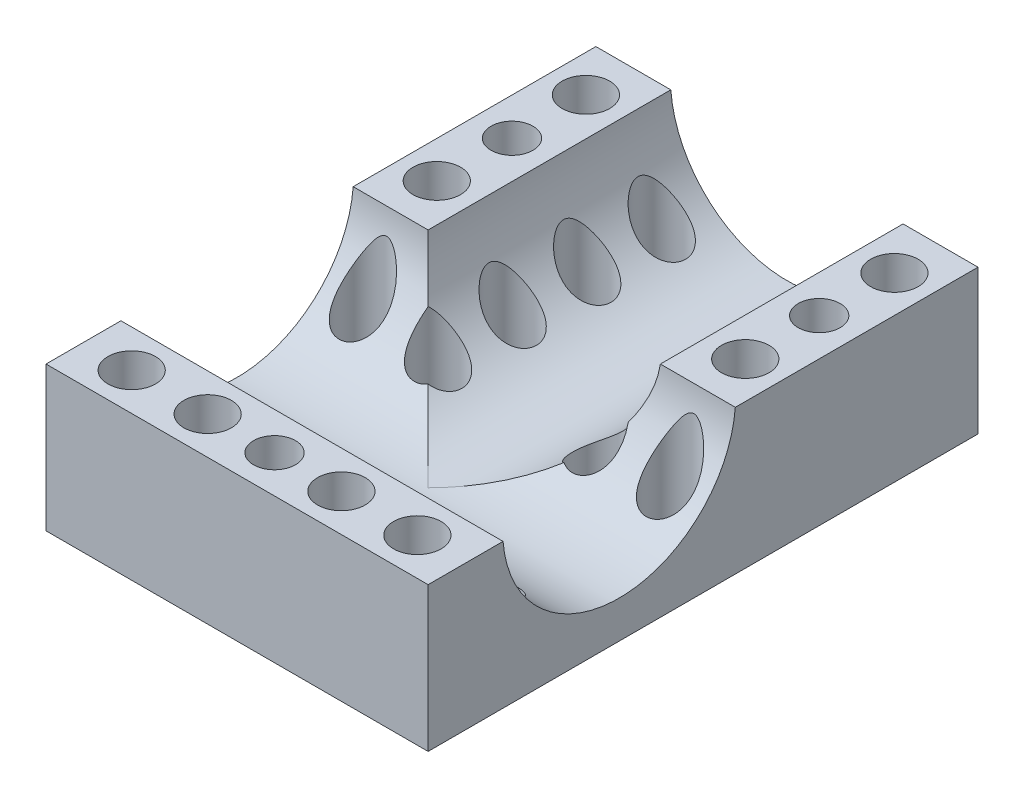
SolidWorks part; units mm, degrees
material "3.1355 (EN-AW 2024)"
ref_plane "Front" through (0, 0, 0) normal (0, 0, 1) x (1, 0, 0)
ref_plane "Top" through (0, 0, 0) normal (0, 1, 0) x (1, 0, 0)
ref_plane "Right" through (0, 0, 0) normal (1, 0, 0) x (0, 0, -1)
sketch "Эскиз1" plane through (0, 0, 0) normal (0, 1, 0) x (1, 0, 0)
  line L0 (0, 0) -> (8, 0)
  line L1 (8, 0) -> (33, 0)
  line L2 (33, 0) -> (41, 0)
  line L3 (0, 0) -> (0, 8)
  line L4 (0, 8) -> (0, 33)
  line L5 (0, 33) -> (0, 41)
  line L6 (0, 41) -> (0, 51)
  line L7 (0, 51) -> (0, 59)
  line L8 (0, 59) -> (41, 59)
  line L9 (41, 59) -> (41, 0)
  dimension "D1" = 8
  dimension "D2" = 25
  dimension "D3" = 8
  dimension "D4" = 8
  dimension "D5" = 25
  dimension "D6" = 8
  dimension "D7" = 10
  dimension "D8" = 8
extrude "Бобышка-Вытянуть1" add sketch "Эскиз1" along normal blind 15.5
sketch "Эскиз4" plane through (0, 0, 0) normal (-1, 0, 0) x (0, 0, 1)
  line L0 (-33, 0) -> (-8, 0) construction
  line L1 (-33, 0) -> (-41, 0) construction
  line L2 (-8, 0) -> (-33, 0) construction
  line L3 (-20.5, 0) -> (-20.5, 16.5) construction
  line L4 (-59, 15.5) -> (0, 15.5) construction
  line L5 (-33, 16.5) -> (-8, 16.5)
  line L6 (-20.5, 16.5) -> (-20.5, 15.5) construction
  arc A0 (-33, 16.5) -> (-8, 16.5) centre (-20.5, 16.5) ccw
  dimension "D1" = 12.5
  dimension "D2" = 1
extrude "Вырез-Вытянуть1" cut sketch "Эскиз4" against normal through all
sketch "Эскиз5" plane through (0, 0, -59) normal (0, 0, -1) x (-1, 0, 0)
  line L0 (-20.5, 16.5) -> (-20.5, 0) construction
  line L2 (0, 0) -> (-41, 0) construction
  line L3 (-33, 16.5) -> (-8, 16.5)
  line L4 (-41, 15.5) -> (0, 15.5) construction
  arc A0 (-33, 16.5) -> (-8, 16.5) centre (-20.5, 16.5) ccw
  dimension "D1" = 12.5
  dimension "D2" = 1
extrude "Вырез-Вытянуть2" cut sketch "Эскиз5" against normal blind 38.5
sketch "Эскиз7" plane through (0, 0, 0) normal (0, -1, 0) x (1, 0, 0)
  line L4 (41, 0) -> (0, 0)
  line L5 (0, 0) -> (0, -59)
  line L6 (0, -59) -> (41, -59)
  line L7 (41, -59) -> (41, 0)
  line L8 (41, 0) -> (0, 0)
  line L9 (0, 0) -> (0, -59)
  line L10 (0, -59) -> (41, -59)
  line L11 (41, -59) -> (41, 0)
  dimension "D1" = 0
ref_plane "Плоскость1" through (0, 4, 0) normal (0, 1, 0) x (1, 0, 0)
sketch "Эскиз6" plane through (0, 4, 0) normal (0, -1, 0) x (1, 0, 0)
  line L0 (20.5, -8.0401) -> (20.5, -32.9599) construction
  line L1 (41, -8.0401) -> (0, -8.0401) construction
  line L2 (0, -32.9599) -> (41, -32.9599) construction
  circle A0 centre (20.5, -20.5) radius 6 construction
  point P11 (20.5, -14.5)
  point P12 (26.5, -20.5)
  point P13 (20.5, -26.5)
  point P14 (14.5, -20.5)
  dimension "D1" = 12
extrude "Бобышка-Вытянуть2" [suppressed] add sketch "Эскиз7" along normal blind 4
sketch "Эскиз14" [suppressed] plane through (0, 2.9, 0) normal (0, 1, 0) x (1, 0, 0)
  circle A0 centre (20.5, 26.5) radius 4
  circle A1 centre (26.5, 20.5) radius 4
  circle A2 centre (20.5, 14.5) radius 4
  circle A3 centre (14.5, 20.5) radius 4
  point P12 (20.5, 20.5)
  dimension "D1" = 8
  dimension "D2" = 4
extrude "Вырез-Вытянуть3" [suppressed] cut sketch "Эскиз14" along normal through all
hole_wizard "Цековка для винта с внутренним шестигранником M44" [suppressed] positions "Эскиз19" profile "Эскиз15" counterbore size "M4" standard "Ansi Metric"
sketch "Эскиз19" [suppressed] plane through (0, 2.9, 0) normal (0, 1, 0) x (1, 0, 0)
  point P0 (14.5, 20.5)
  point P3 (20.5, 26.5)
  point P6 (26.5, 20.5)
  point P9 (20.5, 14.5)
sketch "Эскиз15" plane through (14.5, 2.9, -20.5) normal (1, 0, 0) x (0, 0, 1)
  line L0 (0, 0) -> (0, 6.9)
  line L1 (0, 6.9) -> (2.25, 6.9)
  line L3 (2.25, 6.9) -> (2.25, 4)
  line L4 (2.25, 4) -> (4, 4)
  line L5 (4, 4) -> (4, 0)
  line L7 (4, 0) -> (0, 0)
  line L11 (0, -6.35) -> (0, 107.95) construction
  dimension "Диаметр сквозного отверстия" = 4.5
  dimension "Глубина сквозного отверстия" = 6.9
  dimension "Диаметр цековки" = 8
  dimension "Глубина цековки" = 4
sketch "Эскиз20" plane through (0, 15.5, 0) normal (0, 1, 0) x (1, 0, 0)
  line L1 (4.02, 59) -> (4.02, 32.9599) construction
  line L2 (8.0401, 59) -> (0, 59) construction
  line L3 (0, 32.9599) -> (41, 32.9599) construction
  line L4 (20.5, 59) -> (20.5, 8.0401) construction
  line L5 (32.9599, 59) -> (8.0401, 59) construction
  line L6 (0, 20.5) -> (41, 20.5) construction
  line L7 (0, 32.9599) -> (0, 8.0401) construction
  line L8 (41, 8.0401) -> (41, 32.9599) construction
  line L9 (0, 4.02) -> (41, 4.02) construction
  line L10 (0, 8.0401) -> (0, 0) construction
  line L11 (41, 0) -> (41, 8.0401) construction
  point P17 (4.02, 45.98)
  point P18 (36.98, 45.98)
  point P25 (20.5, 4.02)
  point P26 (-7.3564, 17.7008)
hole_wizard "Отверстие обработанное метчиком M4x0.71" positions "Эскиз22" profile "Эскиз21" tap size "M4x0.7" standard "Ansi Metric" end condition through all
sketch "Эскиз22" plane through (0, 15.5, 0) normal (0, 1, 0) x (1, 0, 0)
  point P0 (4.02, 45.98)
  point P3 (36.98, 45.98)
  point P6 (20.5, 4.02)
sketch "Эскиз21" plane through (4.02, 15.5, -45.98) normal (1, 0, 0) x (0, 0, 1)
  line L0 (0, 0) -> (0, 15.5)
  line L1 (0, 15.5) -> (1.65, 15.5)
  line L2 (1.65, 15.5) -> (1.65, 0)
  line L5 (1.65, 0) -> (0, 0)
  line L11 (0, -6.35) -> (0, 107.95) construction
  dimension "Диаметр проходного сверла" = 3.3
  dimension "Глубина проходного сверла" = 15.5
cosmetic thread "Отверстие резьбы1" parameters "D2"=4
cosmetic thread "Отверстие резьбы2" parameters "D2"=4
cosmetic thread "Отверстие резьбы3" parameters "D2"=4
sketch "Эскиз23" plane through (0, 15.5, 0) normal (0, 1, 0) x (1, 0, 0)
  line L0 (4.02, 59) -> (4.02, 45.98) construction
  line L1 (4.02, 45.98) -> (4.02, 32.9599) construction
  line L2 (20.5, 59) -> (20.5, 8.0401) construction
  line L3 (0, 4.02) -> (18.5, 4.02) construction
  line L4 (0, 4.02) -> (41, 4.02) construction
  line L5 (0, 8.0401) -> (0, 0) construction
  line L6 (4.02, 32.9599) -> (4.02, 29.9806) construction
  line L7 (5.175, 4.02) -> (5.175, 12.02) construction
  line L8 (12.02, 59) -> (12.02, 30.05) construction
  line L9 (32.9599, 59) -> (8.0401, 59) construction
  circle A0 centre (5.175, 4.02) radius 3.175 construction
  circle A1 centre (13.325, 4.02) radius 3.175 construction
  circle A2 centre (27.675, 4.02) radius 3.175 construction
  circle A3 centre (35.825, 4.02) radius 3.175 construction
  point P6 (3.95, 53.9797)
  point P7 (3.95, 37.9803)
  point P12 (37.05, 37.9803)
  point P13 (37.05, 53.9797)
  point P21 (2, 4.02)
  point P26 (8.35, 4.02)
  point P27 (10.15, 4.02)
  point P28 (16.5, 4.02)
  point P33 (36.98, 32.9599)
  point P34 (35.825, 12.02)
  point P37 (36.98, 29.9806)
  point P42 (12.02, 54.05)
  point P43 (12.02, 46.05)
  point P44 (12.02, 38.05)
  point P45 (28.98, 30.05)
  point P46 (28.98, 38.05)
  point P47 (28.98, 46.05)
  point P48 (28.98, 54.05)
  point P49 (27.675, 11.95)
  point P50 (13.325, 11.95)
  point P51 (20.5, 11.95)
  dimension "D2" = 6.35
  dimension "D4" = 6.35
  dimension "D1" = 18.5
  dimension "D3" = 2
  dimension "D5" = 2
  dimension "D6" = 1.8
  dimension "D7" = 8
  dimension "D8" = 8
  dimension "D9" = 8
  dimension "D10" = 8
  dimension "D11" = 8
  dimension "D12" = 8
  dimension "D13" = 8
  dimension "D14" = 8
hole_wizard "Отверстие обработанное метчиком 1/4-201" positions "Эскиз25" profile "Эскиз24" tap size "1/4-20" standard "Ansi Inch" end condition through all
sketch "Эскиз25" plane through (0, 15.5, 0) normal (0, 1, 0) x (1, 0, 0)
  point P0 (3.95, 53.9797)
  point P3 (37.05, 53.9797)
  point P6 (37.05, 37.9803)
  point P9 (3.95, 37.9803)
  point P12 (5.175, 4.02)
  point P15 (13.325, 4.02)
  point P18 (27.675, 4.02)
  point P21 (35.825, 4.02)
sketch "Эскиз24" plane through (3.95, 15.5, -53.9797) normal (1, 0, 0) x (0, 0, 1)
  line L0 (0, 0) -> (0, 15.5)
  line L1 (0, 15.5) -> (2.5527, 15.5)
  line L2 (2.5527, 15.5) -> (2.5527, 0)
  line L5 (2.5527, 0) -> (0, 0)
  line L11 (0, -6.35) -> (0, 107.95) construction
  dimension "Диаметр проходного сверла" = 5.1054
  dimension "Глубина проходного сверла" = 15.5
cosmetic thread "Отверстие резьбы4" parameters "D2"=6.35
cosmetic thread "Отверстие резьбы5" parameters "D2"=6.35
cosmetic thread "Отверстие резьбы6" parameters "D2"=6.35
cosmetic thread "Отверстие резьбы7" parameters "D2"=6.35
cosmetic thread "Отверстие резьбы8" parameters "D2"=6.35
cosmetic thread "Отверстие резьбы9" parameters "D2"=6.35
cosmetic thread "Отверстие резьбы10" parameters "D2"=6.35
cosmetic thread "Отверстие резьбы11" parameters "D2"=6.35
hole_wizard "Отверстие обработанное метчиком 1/4-202" positions "Эскиз28" profile "Эскиз27" tap size "1/4-20" standard "Ansi Inch" end condition through all
sketch "Эскиз28" plane through (0, 15.5, 0) normal (0, 1, 0) x (1, 0, 0)
  point P0 (4.02, 29.9806)
  point P3 (36.98, 29.9806)
  point P6 (35.825, 12.02)
  point P9 (5.175, 12.02)
sketch "Эскиз27" plane through (4.02, 15.5, -29.9806) normal (1, 0, 0) x (0, 0, 1)
  line L0 (0, 0) -> (0, 15.5)
  line L1 (0, 15.5) -> (2.5527, 15.5)
  line L2 (2.5527, 15.5) -> (2.5527, 0)
  line L5 (2.5527, 0) -> (0, 0)
  line L11 (0, -6.35) -> (0, 107.95) construction
  dimension "Диаметр проходного сверла" = 5.1054
  dimension "Глубина проходного сверла" = 15.5
cosmetic thread "Отверстие резьбы12" parameters "D2"=6.35
cosmetic thread "Отверстие резьбы13" parameters "D2"=6.35
cosmetic thread "Отверстие резьбы14" parameters "D2"=6.35
cosmetic thread "Отверстие резьбы15" parameters "D2"=6.35
hole_wizard "Отверстие обработанное метчиком 1/4-203" positions "Эскиз30" profile "Эскиз29" tap size "1/4-20" standard "Ansi Inch" end condition through all
sketch "Эскиз30" plane through (0, 15.5, 0) normal (0, 1, 0) x (1, 0, 0)
  point P0 (12.02, 54.05)
  point P3 (12.02, 46.05)
  point P6 (12.02, 38.05)
  point P9 (12.02, 30.05)
  point P12 (28.98, 54.05)
  point P15 (28.98, 46.05)
  point P18 (28.98, 38.05)
  point P21 (28.98, 30.05)
sketch "Эскиз29" plane through (12.02, 15.5, -54.05) normal (1, 0, 0) x (0, 0, 1)
  line L0 (0, 0) -> (0, 15.5)
  line L1 (0, 15.5) -> (2.5527, 15.5)
  line L2 (2.5527, 15.5) -> (2.5527, 0)
  line L5 (2.5527, 0) -> (0, 0)
  line L11 (0, -6.35) -> (0, 107.95) construction
  dimension "Диаметр проходного сверла" = 5.1054
  dimension "Глубина проходного сверла" = 15.5
cosmetic thread "Отверстие резьбы16" parameters "D2"=6.35
cosmetic thread "Отверстие резьбы17" parameters "D2"=6.35
cosmetic thread "Отверстие резьбы18" parameters "D2"=6.35
cosmetic thread "Отверстие резьбы19" parameters "D2"=6.35
cosmetic thread "Отверстие резьбы20" parameters "D2"=6.35
cosmetic thread "Отверстие резьбы21" parameters "D2"=6.35
cosmetic thread "Отверстие резьбы22" parameters "D2"=6.35
cosmetic thread "Отверстие резьбы23" parameters "D2"=6.35
sketch "Эскиз31" plane through (0, 0, 0) normal (0, -1, 0) x (1, 0, 0)
  circle A0 centre (4.02, -45.98) radius 2.25
  circle A1 centre (36.98, -45.98) radius 2.25
  circle A2 centre (20.5, -4.02) radius 2.25
  dimension "D1" = 4.5
  dimension "D2" = 4.5
  dimension "D3" = 4.5
extrude "Вырез-Вытянуть4" cut sketch "Эскиз31" against normal through all
hole_wizard "Отверстие обработанное метчиком 1/4-204" positions "Эскиз33" profile "Эскиз32" tap size "1/4-20" standard "Ansi Inch" end condition through all
sketch "Эскиз33" plane through (0, 15.5, 0) normal (0, 1, 0) x (1, 0, 0)
  point P0 (27.675, 11.95)
  point P3 (13.325, 11.95)
  point P7 (20.5, 11.95)
sketch "Эскиз32" plane through (27.675, 15.5, -11.95) normal (1, 0, 0) x (0, 0, 1)
  line L0 (0, 0) -> (0, 15.5)
  line L1 (0, 15.5) -> (2.5527, 15.5)
  line L2 (2.5527, 15.5) -> (2.5527, 0)
  line L5 (2.5527, 0) -> (0, 0)
  line L11 (0, -6.35) -> (0, 107.95) construction
  dimension "Диаметр проходного сверла" = 5.1054
  dimension "Глубина проходного сверла" = 15.5
cosmetic thread "Отверстие резьбы24" parameters "D2"=6.35
cosmetic thread "Отверстие резьбы25" parameters "D2"=6.35
cosmetic thread "Отверстие резьбы26" parameters "D2"=6.35
equation "\"D1@Вырез-Вытянуть2\"=25.9+12.6"
equation "\"D4@Эскиз23\"=\"D2@Эскиз23\""
equation "\"D5@Эскиз23\"=\"D3@Эскиз23\""
equation "\"D2@Эскиз31\"=\"D1@Эскиз31\""
equation "\"D3@Эскиз31\"=\"D1@Эскиз31\""
